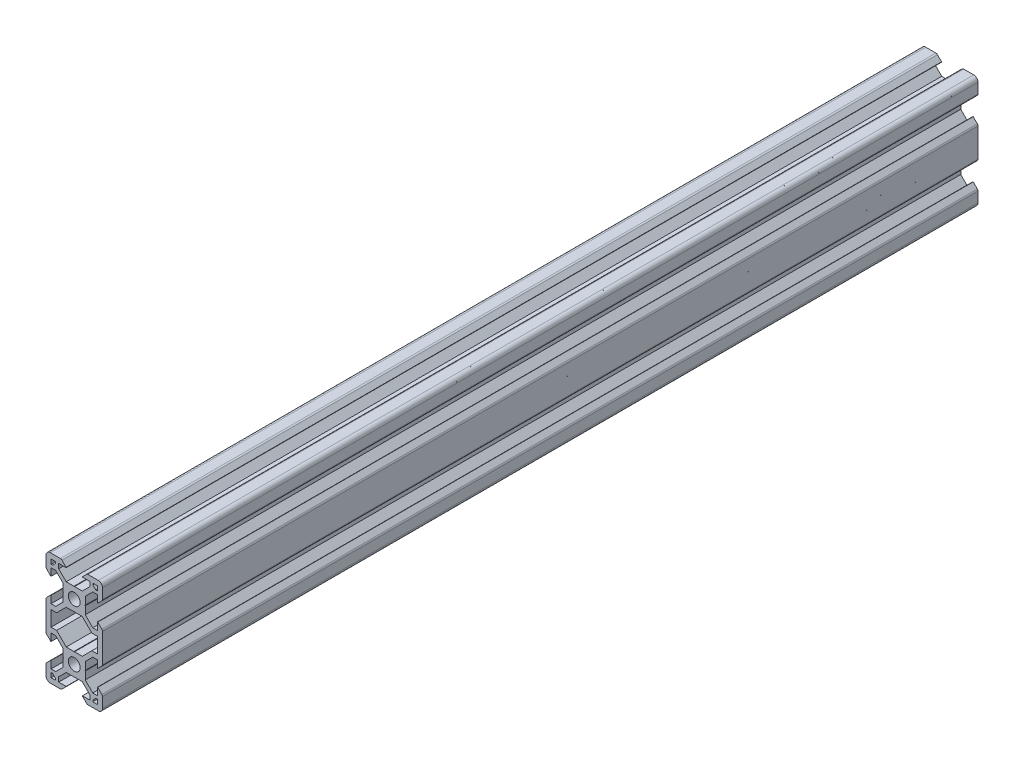
SolidWorks part; units mm, degrees
ref_plane "Front Plane" through (0, 0, 0) normal (0, 0, 1) x (1, 0, 0)
ref_plane "Top Plane" through (0, 0, 0) normal (0, 1, 0) x (1, 0, 0)
ref_plane "Right Plane" through (0, 0, 0) normal (1, 0, 0) x (0, 0, -1)
sketch "Sketch1" plane through (0, 0, 0) normal (0, 0, 1) x (1, 0, 0)
  line L0 (-8.2, 2.8875) -> (-8.2, 5.4975)
  line L3 (-4.9072, 9.9975) -> (-8.5, 9.9975)
  line L4 (-10, 4.9047) -> (-10, 8.4975)
  line L5 (-2.1, 0) -> (-3.8, 0) construction
  line L6 (0, 3.8) -> (0, 0) construction
  line L7 (-0.1, 3.9) -> (-2.8404, 3.9)
  line L8 (-3.9, 0.1) -> (-3.9, 2.8383)
  line L9 (-2.89, 8.1975) -> (-5.5, 8.1975)
  line L10 (-6.57, 8.1975) -> (-6.57, 7.6575)
  line L11 (-8.2, 6.5675) -> (-7.66, 6.5675)
  line L12 (-5.5, 8.1975) -> (-5.5, 6.5588)
  line L13 (-6.56, 5.4975) -> (-8.2, 5.4975)
  line L14 (-8.2, 8.1975) -> (-1.4852, 1.4847) construction
  line L15 (-6.56, 5.4975) -> (-3.9, 2.8383)
  line L16 (-5.5, 6.5588) -> (-2.8404, 3.9)
  line L17 (-7.66, 6.5675) -> (-6.57, 7.6575)
  line L18 (-8.7302, 7.6671) -> (-0.5302, -0.5304) construction
  line L19 (-7.6698, 8.7279) -> (0.5302, 0.5304) construction
  line L20 (-8.2, 8.1975) -> (0, 0) construction
  line L21 (-8.2, 6.5675) -> (-8.2, 8.1975)
  line L22 (-8.2, -0.0025) -> (-8.2, 8.1975) construction
  line L23 (-6.57, 8.1975) -> (-8.2, 8.1975)
  line L24 (0, 8.1975) -> (-8.2, 8.1975) construction
  line L25 (-10, -0.0025) -> (-10, 9.9975) construction
  line L26 (0, 9.9975) -> (-10, 9.9975) construction
  line L27 (-2.89, 8.3075) -> (-2.89, 8.1975)
  line L29 (-8.31, 2.8875) -> (-8.2, 2.8875)
  line L30 (-4.3486, 9.7661) -> (-2.89, 8.3075)
  line L31 (-8.31, 2.8875) -> (-9.7686, 4.3461)
  line L34 (-0.1, 3.9) -> (0, 3.8)
  line L35 (-3.9, 0.1) -> (-3.8, 0)
  line L36 (-8.2, -7.2996) -> (-6.24, -7.2996)
  line L37 (0, 0) -> (0, -10) construction
  line L38 (-0.1, -3.9) -> (-2.8404, -3.9)
  line L39 (-3.8, 0) -> (-3.9, -0.1)
  line L40 (-3.9, -0.1) -> (-3.9, -2.84)
  line L41 (-2.8404, -3.9) -> (-6.24, -7.2996)
  line L42 (-3.9, -2.84) -> (-6.56, -5.5)
  line L43 (-8.2, -2.89) -> (-8.2, -5.5)
  line L44 (-6.56, 5.4975) -> (-6.56, -5.5) construction
  line L45 (-6.56, -5.5) -> (-8.2, -5.5)
  line L46 (-0.1, -3.9) -> (0, -3.8)
  line L48 (-8.2, -2.89) -> (-8.31, -2.89)
  line L49 (-8.31, -2.89) -> (-9.7657, -4.3457)
  line L52 (-10, -10) -> (0, -10) construction
  line L53 (-8.2, -7.2996) -> (-8.2, -10)
  line L61 (-10, -4.9114) -> (-10, -10)
  arc A1 (-10, 8.4975) -> (-8.5, 9.9975) centre (-8.5, 8.4975) cw
  arc A2 (-9.7686, 4.3461) -> (-10, 4.9047) centre (-9.21, 4.9047) cw
  arc A3 (-4.3486, 9.7661) -> (-4.9072, 9.9975) centre (-4.9072, 9.2075) ccw
  arc A4 (-9.7657, -4.3457) -> (-10, -4.9114) centre (-9.2, -4.9114) ccw
  arc A6 (0, 2.1) -> (0, -2.1) centre (0, 0) ccw
  point P29 (-10, 9.9975)
  point P39 (-10, 4.5775)
  point P42 (-4.58, 9.9975)
  point P48 (-10, -4.58)
  dimension "D15" = 1.5
  dimension "D22" = 0.79
  dimension "D30" = 1.96
  dimension "D31" = 2.1
  dimension "D39" = 0.8
  dimension "D4" = 1.8
  dimension "D5" = 3.43
  dimension "D6" = 3.43
  dimension "D7" = 0.54
  dimension "D8" = 0.54
  dimension "D9" = 1.07
  dimension "D10" = 1.07
  dimension "D11" = 3.9
  dimension "D12" = 3.9
  dimension "D16" = 7.11
  dimension "D17" = 0.11
  dimension "D18" = 1.69
  dimension "D19" = 0.11
  dimension "D20" = 7.11
  dimension "D21" = 1.69
  dimension "D23" = 10
  dimension "D24" = 0.1
  dimension "D25" = 45
  dimension "D26" = 0.1
  dimension "D27" = 45
  dimension "D28" = 1.64
  dimension "D29" = 10
  dimension "D32" = 3.9
  dimension "D33" = 45
  dimension "D34" = 2.74
  dimension "D35" = 45
  dimension "D37" = 2.61
  dimension "D38" = 90
  dimension "D40" = 0.1
  dimension "D41" = 45
  dimension "D13" = 0.75
  dimension "D14" = 0.75
sketch "Sketch2" plane through (0, 0, 0) normal (0, 0, 1) x (1, 0, 0)
  line L0 (-0.1, 3.9) -> (0, 3.8) construction
  line L1 (-0.1, 3.9) -> (-2.8404, 3.9) construction
  line L2 (-5.5, 6.5588) -> (-2.8404, 3.9) construction
  line L3 (-5.5, 8.1975) -> (-5.5, 6.5588) construction
  line L4 (-2.89, 8.1975) -> (-5.5, 8.1975) construction
  line L5 (-7.66, 6.5675) -> (-6.57, 7.6575)
  line L6 (-6.57, 7.6575) -> (-6.57, 8.1975)
  line L7 (-6.57, 8.1975) -> (-8.2, 8.1975)
  line L8 (-8.2, 8.1975) -> (-8.2, 6.5675)
  line L9 (-8.2, 6.5675) -> (-7.66, 6.5675)
  line L10 (-7.66, 6.5675) -> (-6.57, 7.6575)
  line L11 (-6.57, 7.6575) -> (-6.57, 8.1975)
  line L12 (-6.57, 8.1975) -> (-8.2, 8.1975)
  line L13 (-8.2, 8.1975) -> (-8.2, 6.5675)
  line L14 (-8.2, 6.5675) -> (-7.66, 6.5675)
  line L15 (-2.89, 8.3075) -> (-2.89, 8.1975) construction
  line L16 (-4.3486, 9.7661) -> (-2.89, 8.3075) construction
  line L17 (-4.9072, 9.9975) -> (-8.5, 9.9975) construction
  line L18 (-10, 4.9047) -> (-10, 8.4975) construction
  line L19 (-8.31, 2.8875) -> (-9.7686, 4.3461) construction
  line L20 (-8.31, 2.8875) -> (-8.2, 2.8875) construction
  line L21 (-8.2, 2.8875) -> (-8.2, 5.4975) construction
  line L22 (-6.56, 5.4975) -> (-8.2, 5.4975) construction
  line L23 (-6.56, 5.4975) -> (-3.9, 2.8383) construction
  line L24 (-3.9, 0.1) -> (-3.9, 2.8383) construction
  line L25 (-3.9, 0.1) -> (-3.8, 0) construction
  line L26 (-3.8, 0) -> (-3.9, -0.1) construction
  line L27 (-3.9, -0.1) -> (-3.9, -2.84) construction
  line L28 (-3.9, -2.84) -> (-6.56, -5.5) construction
  line L29 (-6.56, -5.5) -> (-8.2, -5.5) construction
  line L30 (-8.2, -2.89) -> (-8.2, -5.5) construction
  line L31 (-8.2, -2.89) -> (-8.31, -2.89) construction
  line L32 (-8.31, -2.89) -> (-9.7657, -4.3457) construction
  line L33 (-10, -4.9114) -> (-10, -10) construction
  line L34 (-0.1, -3.9) -> (0, -3.8) construction
  line L35 (-0.1, -3.9) -> (-2.8404, -3.9) construction
  line L36 (-2.8404, -3.9) -> (-6.24, -7.2996) construction
  line L37 (-8.2, -7.2996) -> (-6.24, -7.2996) construction
  line L38 (-8.2, -7.2996) -> (-8.2, -10) construction
  line L39 (-0.1, 3.9) -> (0, 3.8)
  line L40 (-0.1, 3.9) -> (-2.8404, 3.9)
  line L41 (-5.5, 6.5588) -> (-2.8404, 3.9)
  line L42 (-5.5, 8.1975) -> (-5.5, 6.5588)
  line L43 (-2.89, 8.1975) -> (-5.5, 8.1975)
  line L44 (-2.89, 8.3075) -> (-2.89, 8.1975)
  line L45 (-4.3486, 9.7661) -> (-2.89, 8.3075)
  line L46 (-4.9072, 9.9975) -> (-8.5, 9.9975)
  line L47 (-10, 4.9047) -> (-10, 8.4975)
  line L48 (-8.31, 2.8875) -> (-9.7686, 4.3461)
  line L49 (-8.31, 2.8875) -> (-8.2, 2.8875)
  line L50 (-8.2, 2.8875) -> (-8.2, 5.4975)
  line L51 (-6.56, 5.4975) -> (-8.2, 5.4975)
  line L52 (-6.56, 5.4975) -> (-3.9, 2.8383)
  line L53 (-3.9, 0.1) -> (-3.9, 2.8383)
  line L54 (-3.9, 0.1) -> (-3.8, 0)
  line L55 (-3.8, 0) -> (-3.9, -0.1)
  line L56 (-3.9, -0.1) -> (-3.9, -2.84)
  line L57 (-3.9, -2.84) -> (-6.56, -5.5)
  line L58 (-6.56, -5.5) -> (-8.2, -5.5)
  line L59 (-8.2, -2.89) -> (-8.2, -5.5)
  line L60 (-8.2, -2.89) -> (-8.31, -2.89)
  line L61 (-8.31, -2.89) -> (-9.7657, -4.3457)
  line L62 (-10, -4.9114) -> (-10, -15.0886)
  line L63 (-0.1, -3.9) -> (0, -3.8)
  line L64 (-0.1, -3.9) -> (-2.8404, -3.9)
  line L65 (-2.8404, -3.9) -> (-6.24, -7.2996)
  line L66 (-8.2, -7.2996) -> (-6.24, -7.2996)
  line L67 (-8.2, -7.2996) -> (-8.2, -12.7004)
  line L68 (0, 0) -> (0, -10) construction
  line L69 (-10, -10) -> (0, -10) construction
  line L70 (0, 0) -> (0, -20) construction
  line L71 (-10, -10) -> (10, -10) construction
  line L72 (8.2, -7.2996) -> (8.2, -12.7004)
  line L73 (8.2, -7.2996) -> (6.24, -7.2996)
  line L74 (2.8404, -3.9) -> (6.24, -7.2996)
  line L75 (0.1, -3.9) -> (2.8404, -3.9)
  line L76 (0.1, -3.9) -> (0, -3.8)
  line L77 (10, -4.9114) -> (10, -15.0886)
  line L78 (8.31, -2.89) -> (9.7657, -4.3457)
  line L79 (8.2, -2.89) -> (8.31, -2.89)
  line L80 (8.2, -2.89) -> (8.2, -5.5)
  line L81 (6.56, -5.5) -> (8.2, -5.5)
  line L82 (3.9, -2.84) -> (6.56, -5.5)
  line L83 (3.9, -0.1) -> (3.9, -2.84)
  line L84 (3.8, 0) -> (3.9, -0.1)
  line L85 (3.9, 0.1) -> (3.8, 0)
  line L86 (3.9, 0.1) -> (3.9, 2.8383)
  line L87 (6.56, 5.4975) -> (3.9, 2.8383)
  line L88 (6.56, 5.4975) -> (8.2, 5.4975)
  line L89 (8.2, 2.8875) -> (8.2, 5.4975)
  line L90 (8.31, 2.8875) -> (8.2, 2.8875)
  line L91 (8.31, 2.8875) -> (9.7686, 4.3461)
  line L92 (10, 4.9047) -> (10, 8.4975)
  line L93 (4.9072, 9.9975) -> (8.5, 9.9975)
  line L94 (4.3486, 9.7661) -> (2.89, 8.3075)
  line L95 (2.89, 8.3075) -> (2.89, 8.1975)
  line L96 (2.89, 8.1975) -> (5.5, 8.1975)
  line L97 (5.5, 8.1975) -> (5.5, 6.5588)
  line L98 (5.5, 6.5588) -> (2.8404, 3.9)
  line L99 (0.1, 3.9) -> (2.8404, 3.9)
  line L100 (0.1, 3.9) -> (0, 3.8)
  line L101 (8.2, 6.5675) -> (7.66, 6.5675)
  line L102 (8.2, 8.1975) -> (8.2, 6.5675)
  line L103 (6.57, 8.1975) -> (8.2, 8.1975)
  line L104 (6.57, 7.6575) -> (6.57, 8.1975)
  line L105 (7.66, 6.5675) -> (6.57, 7.6575)
  line L106 (7.66, -26.5675) -> (6.57, -27.6575)
  line L107 (6.57, -27.6575) -> (6.57, -28.1975)
  line L108 (6.57, -28.1975) -> (8.2, -28.1975)
  line L109 (8.2, -28.1975) -> (8.2, -26.5675)
  line L110 (8.2, -26.5675) -> (7.66, -26.5675)
  line L111 (0.1, -23.9) -> (0, -23.8)
  line L112 (0.1, -23.9) -> (2.8404, -23.9)
  line L113 (5.5, -26.5588) -> (2.8404, -23.9)
  line L114 (5.5, -28.1975) -> (5.5, -26.5588)
  line L115 (2.89, -28.1975) -> (5.5, -28.1975)
  line L116 (2.89, -28.3075) -> (2.89, -28.1975)
  line L117 (4.3486, -29.7661) -> (2.89, -28.3075)
  line L118 (4.9072, -29.9975) -> (8.5, -29.9975)
  line L119 (10, -24.9047) -> (10, -28.4975)
  line L120 (8.31, -22.8875) -> (9.7686, -24.3461)
  line L121 (8.31, -22.8875) -> (8.2, -22.8875)
  line L122 (8.2, -22.8875) -> (8.2, -25.4975)
  line L123 (6.56, -25.4975) -> (8.2, -25.4975)
  line L124 (6.56, -25.4975) -> (3.9, -22.8383)
  line L125 (3.9, -20.1) -> (3.9, -22.8383)
  line L126 (3.9, -20.1) -> (3.8, -20)
  line L127 (3.8, -20) -> (3.9, -19.9)
  line L128 (3.9, -19.9) -> (3.9, -17.16)
  line L129 (3.9, -17.16) -> (6.56, -14.5)
  line L130 (6.56, -14.5) -> (8.2, -14.5)
  line L131 (8.2, -17.11) -> (8.2, -14.5)
  line L132 (8.2, -17.11) -> (8.31, -17.11)
  line L133 (8.31, -17.11) -> (9.7657, -15.6543)
  line L134 (0.1, -16.1) -> (0, -16.2)
  line L135 (0.1, -16.1) -> (2.8404, -16.1)
  line L136 (2.8404, -16.1) -> (6.24, -12.7004)
  line L137 (8.2, -12.7004) -> (6.24, -12.7004)
  line L138 (-8.2, -12.7004) -> (-6.24, -12.7004)
  line L139 (-2.8404, -16.1) -> (-6.24, -12.7004)
  line L140 (-0.1, -16.1) -> (-2.8404, -16.1)
  line L141 (-0.1, -16.1) -> (0, -16.2)
  line L142 (-8.31, -17.11) -> (-9.7657, -15.6543)
  line L143 (-8.2, -17.11) -> (-8.31, -17.11)
  line L144 (-8.2, -17.11) -> (-8.2, -14.5)
  line L145 (-6.56, -14.5) -> (-8.2, -14.5)
  line L146 (-3.9, -17.16) -> (-6.56, -14.5)
  line L147 (-3.9, -19.9) -> (-3.9, -17.16)
  line L148 (-3.8, -20) -> (-3.9, -19.9)
  line L149 (-3.9, -20.1) -> (-3.8, -20)
  line L150 (-3.9, -20.1) -> (-3.9, -22.8383)
  line L151 (-6.56, -25.4975) -> (-3.9, -22.8383)
  line L152 (-6.56, -25.4975) -> (-8.2, -25.4975)
  line L153 (-8.2, -22.8875) -> (-8.2, -25.4975)
  line L154 (-8.31, -22.8875) -> (-8.2, -22.8875)
  line L155 (-8.31, -22.8875) -> (-9.7686, -24.3461)
  line L156 (-10, -24.9047) -> (-10, -28.4975)
  line L157 (-4.9072, -29.9975) -> (-8.5, -29.9975)
  line L158 (-4.3486, -29.7661) -> (-2.89, -28.3075)
  line L159 (-2.89, -28.3075) -> (-2.89, -28.1975)
  line L160 (-2.89, -28.1975) -> (-5.5, -28.1975)
  line L161 (-5.5, -28.1975) -> (-5.5, -26.5588)
  line L162 (-5.5, -26.5588) -> (-2.8404, -23.9)
  line L163 (-0.1, -23.9) -> (-2.8404, -23.9)
  line L164 (-0.1, -23.9) -> (0, -23.8)
  line L165 (-8.2, -26.5675) -> (-7.66, -26.5675)
  line L166 (-8.2, -28.1975) -> (-8.2, -26.5675)
  line L167 (-6.57, -28.1975) -> (-8.2, -28.1975)
  line L168 (-6.57, -27.6575) -> (-6.57, -28.1975)
  line L169 (-7.66, -26.5675) -> (-6.57, -27.6575)
  arc A0 (0, 2.1) -> (0, -2.1) centre (0, 0) ccw construction
  arc A1 (-4.3486, 9.7661) -> (-4.9072, 9.9975) centre (-4.9072, 9.2075) ccw construction
  arc A2 (-8.5, 9.9975) -> (-10, 8.4975) centre (-8.5, 8.4975) ccw construction
  arc A3 (-10, 4.9047) -> (-9.7686, 4.3461) centre (-9.21, 4.9047) ccw construction
  arc A4 (-9.7657, -4.3457) -> (-10, -4.9114) centre (-9.2, -4.9114) ccw construction
  circle A5 centre (0, 0) radius 2.1
  arc A6 (-4.3486, 9.7661) -> (-4.9072, 9.9975) centre (-4.9072, 9.2075) ccw
  arc A7 (-8.5, 9.9975) -> (-10, 8.4975) centre (-8.5, 8.4975) ccw
  arc A8 (-10, 4.9047) -> (-9.7686, 4.3461) centre (-9.21, 4.9047) ccw
  arc A9 (-9.7657, -4.3457) -> (-10, -4.9114) centre (-9.2, -4.9114) ccw
  arc A10 (9.7657, -4.3457) -> (10, -4.9114) centre (9.2, -4.9114) cw
  arc A11 (10, 4.9047) -> (9.7686, 4.3461) centre (9.21, 4.9047) cw
  arc A12 (8.5, 9.9975) -> (10, 8.4975) centre (8.5, 8.4975) cw
  arc A13 (4.3486, 9.7661) -> (4.9072, 9.9975) centre (4.9072, 9.2075) cw
  arc A14 (4.3486, -29.7661) -> (4.9072, -29.9975) centre (4.9072, -29.2075) ccw
  arc A15 (8.5, -29.9975) -> (10, -28.4975) centre (8.5, -28.4975) ccw
  arc A16 (10, -24.9047) -> (9.7686, -24.3461) centre (9.21, -24.9047) ccw
  arc A17 (9.7657, -15.6543) -> (10, -15.0886) centre (9.2, -15.0886) ccw
  arc A18 (-9.7657, -15.6543) -> (-10, -15.0886) centre (-9.2, -15.0886) cw
  arc A19 (-10, -24.9047) -> (-9.7686, -24.3461) centre (-9.21, -24.9047) cw
  arc A20 (-8.5, -29.9975) -> (-10, -28.4975) centre (-8.5, -28.4975) cw
  arc A21 (-4.3486, -29.7661) -> (-4.9072, -29.9975) centre (-4.9072, -29.2075) cw
  circle A22 centre (0, -20) radius 2.1
  point P147 (8.2, -10)
  dimension "D1" = 0
extrude "Boss-Extrude1" add sketch "Sketch2" against normal blind 310
